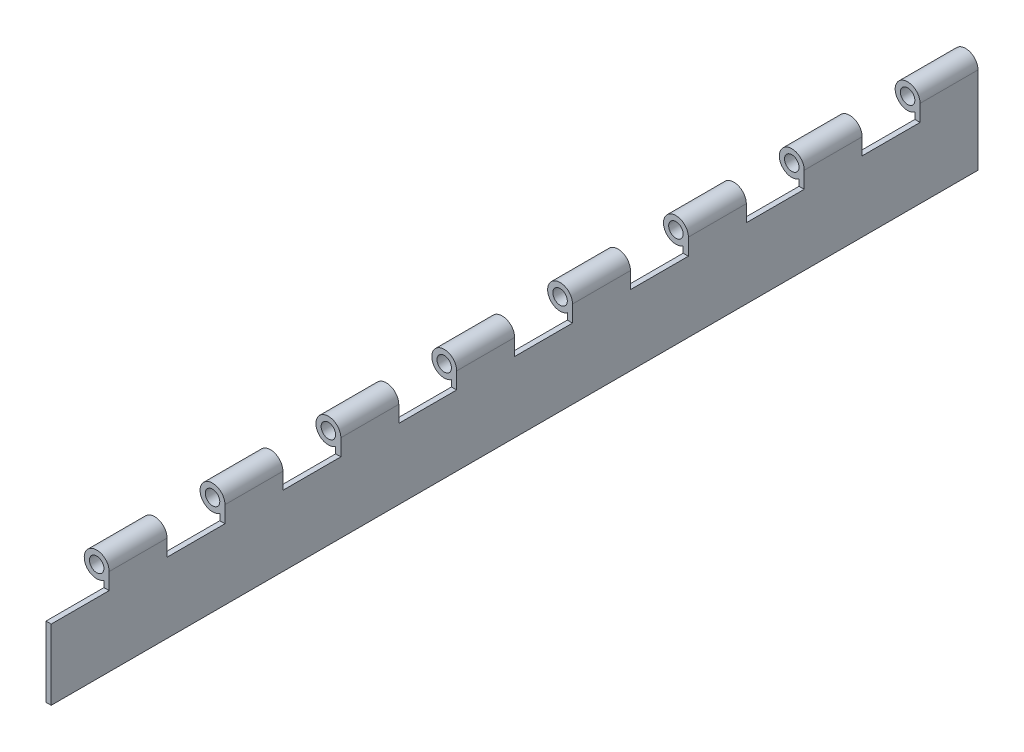
SolidWorks part; units mm, degrees
material "6061 Alloy"
ref_plane "Front Plane" through (0, 0, 0) normal (0, 0, 1) x (1, 0, 0)
ref_plane "Top Plane" through (0, 0, 0) normal (0, 1, 0) x (1, 0, 0)
ref_plane "Right Plane" through (0, 0, 0) normal (1, 0, 0) x (0, 0, -1)
sketch "Sketch1" plane through (0, 0, 0) normal (0, 0, 1) x (1, 0, 0)
  line L0 (5.461, 0) -> (5.461, -38.1)
  line L1 (5.461, -38.1) -> (3.175, -38.1)
  line L2 (3.175, -38.1) -> (3.175, -4.4432)
  circle A0 centre (0, 0) radius 3.175
  arc A1 (5.461, 0) -> (3.175, -4.4432) centre (0, 0) ccw
  circle A2 centre (0, 0) radius 5.461 construction
  dimension "D1" = 6.35
  dimension "D3" = 2.286
  dimension "D4" = 38.1
  dimension "D2" = 2.286
extrude "Boss-Extrude1" add sketch "Sketch1" along normal blind 406.4
sketch "Sketch2" plane through (5.461, 0, 0) normal (1, 0, 0) x (0, 0, -1)
  line L1 (-406.4, 5.461) -> (-381, 5.461)
  line L2 (-406.4, 5.461) -> (-406.4, -7.239)
  line L3 (-406.4, -7.239) -> (-381, -7.239)
  line L4 (-381, 5.461) -> (-381, -7.239)
  dimension "D1" = 12.7
  dimension "D2" = 25.4
extrude "Cut-Extrude1" cut sketch "Sketch2" against normal through all
pattern_linear "LPattern1" count 8 spacing 50.8 along (0, 0, -1) of "Cut-Extrude1"
